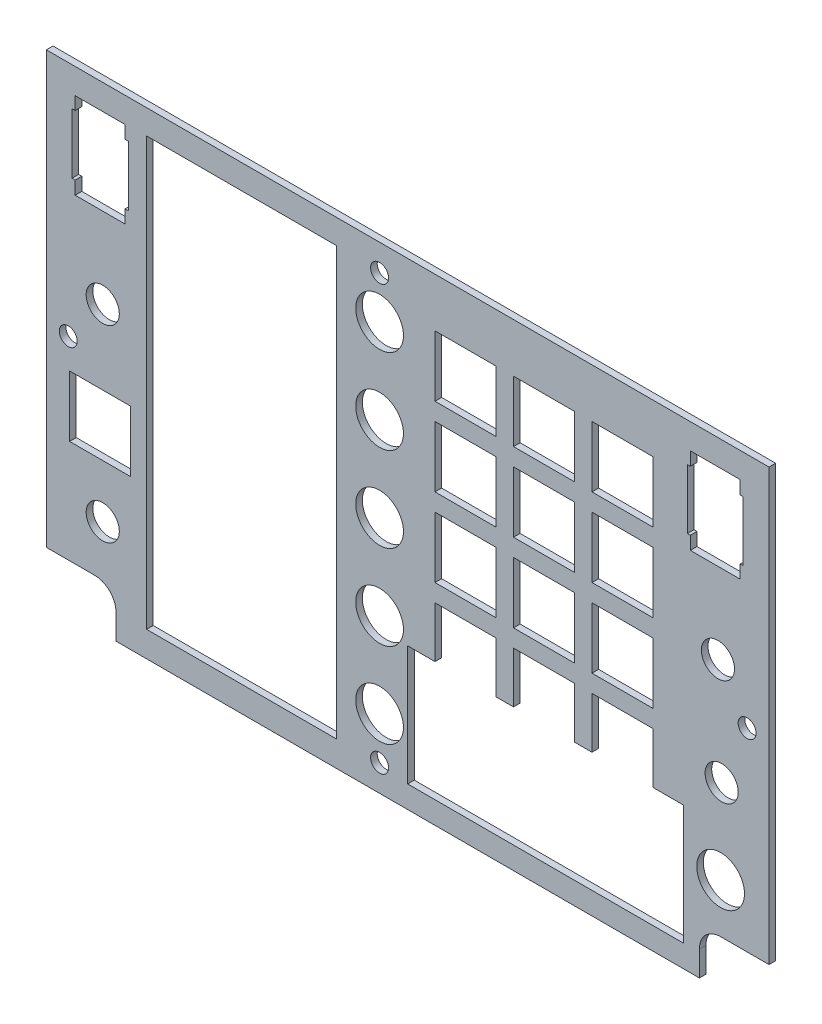
SolidWorks part; units mm, degrees
material "ABS PC"
ref_plane "Front Plane" through (0, 0, 0) normal (0, 0, 1) x (1, 0, 0)
ref_plane "Top Plane" through (0, 0, 0) normal (0, 1, 0) x (1, 0, 0)
ref_plane "Right Plane" through (0, 0, 0) normal (1, 0, 0) x (0, 0, -1)
sketch "Sketch1" plane through (0, 0, 0) normal (0, 0, 1) x (1, 0, 0)
  line L8 (74.93, -171.1167) -> (86.5187, -171.1167)
  line L9 (86.5187, -171.1167) -> (86.5187, -67.9292)
  line L10 (86.5187, -67.9292) -> (-86.5187, -67.9292)
  line L11 (-86.5187, -67.9292) -> (-86.5187, -171.1167)
  line L12 (-86.5187, -171.1167) -> (-74.93, -171.1167)
  line L13 (-69.85, -176.1967) -> (-69.85, -182.2292)
  line L14 (-69.85, -182.2292) -> (69.85, -182.2292)
  line L15 (69.85, -182.2292) -> (69.85, -176.1967)
  line L16 (74.93, -171.1167) -> (86.5187, -171.1167)
  line L17 (86.5187, -171.1167) -> (86.5187, -67.9292)
  line L18 (86.5187, -67.9292) -> (-86.5187, -67.9292)
  line L19 (-86.5187, -67.9292) -> (-86.5187, -171.1167)
  line L20 (-86.5187, -171.1167) -> (-74.93, -171.1167)
  line L21 (-69.85, -176.1967) -> (-69.85, -182.2292)
  line L22 (-69.85, -182.2292) -> (69.85, -182.2292)
  line L23 (69.85, -182.2292) -> (69.85, -176.1967)
  arc A2 (-69.85, -176.1967) -> (-74.93, -171.1167) centre (-74.93, -176.1967) ccw
  arc A3 (74.93, -171.1167) -> (69.85, -176.1967) centre (74.93, -176.1967) ccw
  arc A4 (-69.85, -176.1967) -> (-74.93, -171.1167) centre (-74.93, -176.1967) ccw
  arc A5 (74.93, -171.1167) -> (69.85, -176.1967) centre (74.93, -176.1967) ccw
  dimension "D1" = 0
extrude "Boss-Extrude1" add sketch "Sketch1" against normal blind 1.5875
sketch "Sketch3" plane through (0, 0, 0) normal (0, 0, 1) x (1, 0, 0)
  line L0 (-67.6275, -133.0167) -> (-79.6925, -133.0167) construction
  line L1 (-79.6925, -133.0167) -> (-79.6925, -145.0817) construction
  line L2 (-79.6925, -145.0817) -> (-67.6275, -145.0817) construction
  line L3 (-67.6275, -145.0817) -> (-67.6275, -133.0167) construction
  line L4 (19.8755, -149.3997) -> (19.8755, -137.3347) construction
  line L5 (19.8755, -137.3347) -> (7.8105, -137.3347) construction
  line L6 (7.8105, -137.3347) -> (7.8105, -149.3997) construction
  line L7 (7.8105, -149.3997) -> (19.8755, -149.3997) construction
  line L8 (38.6715, -149.3997) -> (38.6715, -137.3347) construction
  line L9 (38.6715, -137.3347) -> (26.6065, -137.3347) construction
  line L10 (26.6065, -137.3347) -> (26.6065, -149.3997) construction
  line L11 (26.6065, -149.3997) -> (38.6715, -149.3997) construction
  line L12 (45.4025, -149.3997) -> (57.4675, -149.3997) construction
  line L13 (57.4675, -149.3997) -> (57.4675, -137.3347) construction
  line L14 (57.4675, -137.3347) -> (45.4025, -137.3347) construction
  line L15 (45.4025, -137.3347) -> (45.4025, -149.3997) construction
  line L16 (57.4675, -130.6037) -> (57.4675, -118.5387) construction
  line L17 (57.4675, -118.5387) -> (45.4025, -118.5387) construction
  line L18 (45.4025, -118.5387) -> (45.4025, -130.6037) construction
  line L19 (45.4025, -130.6037) -> (57.4675, -130.6037) construction
  line L20 (38.6715, -130.6037) -> (38.6715, -118.5387) construction
  line L21 (38.6715, -118.5387) -> (26.6065, -118.5387) construction
  line L22 (26.6065, -118.5387) -> (26.6065, -130.6037) construction
  line L23 (26.6065, -130.6037) -> (38.6715, -130.6037) construction
  line L24 (19.8755, -130.6037) -> (19.8755, -118.5387) construction
  line L25 (19.8755, -118.5387) -> (7.8105, -118.5387) construction
  line L26 (7.8105, -118.5387) -> (7.8105, -130.6037) construction
  line L27 (7.8105, -130.6037) -> (19.8755, -130.6037) construction
  line L28 (19.8755, -111.8077) -> (19.8755, -99.7427) construction
  line L29 (19.8755, -99.7427) -> (7.8105, -99.7427) construction
  line L30 (7.8105, -99.7427) -> (7.8105, -111.8077) construction
  line L31 (7.8105, -111.8077) -> (19.8755, -111.8077) construction
  line L32 (19.8755, -93.0117) -> (19.8755, -80.9467) construction
  line L33 (19.8755, -80.9467) -> (7.8105, -80.9467) construction
  line L34 (7.8105, -80.9467) -> (7.8105, -93.0117) construction
  line L35 (7.8105, -93.0117) -> (19.8755, -93.0117) construction
  line L36 (38.6715, -93.0117) -> (38.6715, -80.9467) construction
  line L37 (38.6715, -80.9467) -> (26.6065, -80.9467) construction
  line L38 (26.6065, -80.9467) -> (26.6065, -93.0117) construction
  line L39 (26.6065, -93.0117) -> (38.6715, -93.0117) construction
  line L40 (38.6715, -111.8077) -> (38.6715, -99.7427) construction
  line L41 (38.6715, -99.7427) -> (26.6065, -99.7427) construction
  line L42 (26.6065, -99.7427) -> (26.6065, -111.8077) construction
  line L43 (26.6065, -111.8077) -> (38.6715, -111.8077) construction
  line L44 (57.4675, -111.8077) -> (57.4675, -99.7427) construction
  line L45 (57.4675, -99.7427) -> (45.4025, -99.7427) construction
  line L46 (45.4025, -99.7427) -> (45.4025, -111.8077) construction
  line L47 (45.4025, -111.8077) -> (57.4675, -111.8077) construction
  line L48 (57.4675, -93.0117) -> (57.4675, -80.9467) construction
  line L49 (57.4675, -80.9467) -> (45.4025, -80.9467) construction
  line L50 (45.4025, -80.9467) -> (45.4025, -93.0117) construction
  line L51 (45.4025, -93.0117) -> (57.4675, -93.0117) construction
  line L52 (-67.6275, -133.0167) -> (-79.6925, -133.0167)
  line L53 (-79.6925, -133.0167) -> (-79.6925, -145.0817)
  line L54 (-79.6925, -145.0817) -> (-67.6275, -145.0817)
  line L55 (-67.6275, -145.0817) -> (-67.6275, -133.0167)
  line L56 (19.8755, -149.3997) -> (19.8755, -137.3347)
  line L57 (19.8755, -137.3347) -> (7.8105, -137.3347)
  line L58 (7.8105, -137.3347) -> (7.8105, -149.3997)
  line L59 (7.8105, -149.3997) -> (19.8755, -149.3997)
  line L60 (38.6715, -149.3997) -> (38.6715, -137.3347)
  line L61 (38.6715, -137.3347) -> (26.6065, -137.3347)
  line L62 (26.6065, -137.3347) -> (26.6065, -149.3997)
  line L63 (26.6065, -149.3997) -> (38.6715, -149.3997)
  line L64 (45.4025, -149.3997) -> (57.4675, -149.3997)
  line L65 (57.4675, -149.3997) -> (57.4675, -137.3347)
  line L66 (57.4675, -137.3347) -> (45.4025, -137.3347)
  line L67 (45.4025, -137.3347) -> (45.4025, -149.3997)
  line L68 (57.4675, -130.6037) -> (57.4675, -118.5387)
  line L69 (57.4675, -118.5387) -> (45.4025, -118.5387)
  line L70 (45.4025, -118.5387) -> (45.4025, -130.6037)
  line L71 (45.4025, -130.6037) -> (57.4675, -130.6037)
  line L72 (38.6715, -130.6037) -> (38.6715, -118.5387)
  line L73 (38.6715, -118.5387) -> (26.6065, -118.5387)
  line L74 (26.6065, -118.5387) -> (26.6065, -130.6037)
  line L75 (26.6065, -130.6037) -> (38.6715, -130.6037)
  line L76 (19.8755, -130.6037) -> (19.8755, -118.5387)
  line L77 (19.8755, -118.5387) -> (7.8105, -118.5387)
  line L78 (7.8105, -118.5387) -> (7.8105, -130.6037)
  line L79 (7.8105, -130.6037) -> (19.8755, -130.6037)
  line L80 (19.8755, -111.8077) -> (19.8755, -99.7427)
  line L81 (19.8755, -99.7427) -> (7.8105, -99.7427)
  line L82 (7.8105, -99.7427) -> (7.8105, -111.8077)
  line L83 (7.8105, -111.8077) -> (19.8755, -111.8077)
  line L84 (19.8755, -93.0117) -> (19.8755, -80.9467)
  line L85 (19.8755, -80.9467) -> (7.8105, -80.9467)
  line L86 (7.8105, -80.9467) -> (7.8105, -93.0117)
  line L87 (7.8105, -93.0117) -> (19.8755, -93.0117)
  line L88 (38.6715, -93.0117) -> (38.6715, -80.9467)
  line L89 (38.6715, -80.9467) -> (26.6065, -80.9467)
  line L90 (26.6065, -80.9467) -> (26.6065, -93.0117)
  line L91 (26.6065, -93.0117) -> (38.6715, -93.0117)
  line L92 (38.6715, -111.8077) -> (38.6715, -99.7427)
  line L93 (38.6715, -99.7427) -> (26.6065, -99.7427)
  line L94 (26.6065, -99.7427) -> (26.6065, -111.8077)
  line L95 (26.6065, -111.8077) -> (38.6715, -111.8077)
  line L96 (57.4675, -111.8077) -> (57.4675, -99.7427)
  line L97 (57.4675, -99.7427) -> (45.4025, -99.7427)
  line L98 (45.4025, -99.7427) -> (45.4025, -111.8077)
  line L99 (45.4025, -111.8077) -> (57.4675, -111.8077)
  line L100 (57.4675, -93.0117) -> (57.4675, -80.9467)
  line L101 (57.4675, -80.9467) -> (45.4025, -80.9467)
  line L102 (45.4025, -80.9467) -> (45.4025, -93.0117)
  line L103 (45.4025, -93.0117) -> (57.4675, -93.0117)
  circle A0 centre (74.93, -159.3692) radius 4.445 construction
  circle A1 centre (-6.731, -165.7192) radius 4.445 construction
  circle A2 centre (-6.731, -145.3992) radius 4.445 construction
  circle A3 centre (-6.731, -125.0792) radius 4.445 construction
  circle A4 centre (-6.731, -104.7592) radius 4.445 construction
  circle A5 centre (-6.731, -84.4392) radius 4.445 construction
  circle A6 centre (74.93, -159.3692) radius 4.445
  circle A7 centre (-6.731, -165.7192) radius 4.445
  circle A8 centre (-6.731, -145.3992) radius 4.445
  circle A9 centre (-6.731, -125.0792) radius 4.445
  circle A10 centre (-6.731, -104.7592) radius 4.445
  circle A11 centre (-6.731, -84.4392) radius 4.445
extrude "Cut-Extrude1" cut sketch "Sketch3" against normal through all
sketch "Sketch4" plane through (0, 0, 0) normal (0, 0, 1) x (1, 0, 0)
  circle A0 centre (-73.025, -113.9667) radius 3.9688
  circle A1 centre (-73.025, -159.0517) radius 3.9688
  circle A2 centre (74.295, -113.9667) radius 3.9688
  circle A3 centre (75.184, -139.0492) radius 3.9687
  dimension "D1" = 7.9375
extrude "Cut-Extrude2" cut sketch "Sketch4" against normal through all
sketch "Sketch5" plane through (0, 0, 0) normal (0, 0, 1) x (1, 0, 0)
  line L0 (-79.63, -73.9922) -> (-79.63, -94.6322)
  line L1 (-79.63, -94.6322) -> (-67.69, -94.6322)
  line L2 (-67.69, -94.6322) -> (-67.69, -73.9922)
  line L3 (-67.69, -73.9922) -> (-79.63, -73.9922)
  line L4 (-78.36, -75.2622) -> (-78.36, -93.3622)
  line L5 (-78.36, -93.3622) -> (-68.96, -93.3622)
  line L6 (-68.96, -93.3622) -> (-68.96, -75.2622)
  line L7 (-68.96, -75.2622) -> (-78.36, -75.2622)
  line L8 (-78.36, -75.2622) -> (-78.36, -93.3622) construction
  line L9 (-78.36, -93.3622) -> (-68.96, -93.3622) construction
  line L10 (-68.96, -93.3622) -> (-68.96, -75.2622) construction
  line L11 (-68.96, -75.2622) -> (-78.36, -75.2622) construction
  line L12 (68.96, -75.2622) -> (68.96, -93.3622)
  line L13 (68.96, -93.3622) -> (78.36, -93.3622)
  line L14 (78.36, -93.3622) -> (78.36, -75.2622)
  line L15 (78.36, -75.2622) -> (68.96, -75.2622)
  line L16 (68.96, -75.2622) -> (68.96, -93.3622) construction
  line L17 (68.96, -93.3622) -> (78.36, -93.3622) construction
  line L18 (78.36, -93.3622) -> (78.36, -75.2622) construction
  line L19 (78.36, -75.2622) -> (68.96, -75.2622) construction
  line L20 (67.69, -73.9922) -> (67.69, -94.6322)
  line L21 (67.69, -94.6322) -> (79.63, -94.6322)
  line L22 (79.63, -94.6322) -> (79.63, -73.9922)
  line L23 (79.63, -73.9922) -> (67.69, -73.9922)
  line L24 (-61.06, -75.0622) -> (-51.66, -75.0622) construction
  line L25 (-62.53, -73.7922) -> (-17.068, -73.7922)
  line L26 (-62.53, -73.7922) -> (-62.53, -176.1122)
  line L27 (-62.53, -176.1122) -> (-17.068, -176.1122)
  line L28 (-17.068, -73.7922) -> (-17.068, -176.1122)
  line L29 (-62.53, -73.7922) -> (-17.068, -176.1122) construction
  line L30 (-62.53, -176.1122) -> (-17.068, -73.7922) construction
  line L31 (-61.26, -93.3622) -> (-61.26, -75.2622) construction
  line L32 (-51.66, -174.8422) -> (-61.06, -174.8422) construction
  line L33 (-18.338, -167.7344) -> (-18.338, -169.4031) construction
  line L34 (61.52, -158.4422) -> (61.52, -172.5422) construction
  line L35 (5.02, -157.9422) -> (61.02, -157.9422) construction
  line L36 (61.02, -173.0422) -> (5.02, -173.0422) construction
  line L37 (4.52, -172.5422) -> (4.52, -158.4422) construction
  line L38 (61.52, -157.9422) -> (61.52, -173.0422)
  line L39 (4.52, -157.9422) -> (61.52, -157.9422)
  line L40 (61.52, -173.0422) -> (4.52, -173.0422)
  line L41 (4.52, -173.0422) -> (4.52, -157.9422)
  point P20 (-39.799, -124.9522)
  dimension "D4" = 1.27
  dimension "D5" = 1.27
  dimension "D6" = 1.27
  dimension "D7" = 1.27
  dimension "D1" = 0
  dimension "D2" = 0
  dimension "D3" = 1.27
extrude "Cut-Extrude3" cut sketch "Sketch5" against normal through all
sketch "Sketch6" plane through (0, 0, 0) normal (0, 0, 1) x (1, 0, 0)
  line L4 (-67.6275, -133.0167) -> (-79.6925, -133.0167) construction
  line L5 (57.4675, -137.3347) -> (45.4025, -137.3347) construction
  line L6 (45.4025, -137.3347) -> (45.4025, -149.3997) construction
  line L7 (45.4025, -149.3997) -> (57.4675, -149.3997) construction
  line L8 (57.4675, -149.3997) -> (57.4675, -137.3347) construction
  line L9 (45.4025, -130.6037) -> (57.4675, -130.6037) construction
  line L10 (57.4675, -130.6037) -> (57.4675, -118.5387) construction
  line L11 (57.4675, -118.5387) -> (45.4025, -118.5387) construction
  line L12 (45.4025, -118.5387) -> (45.4025, -130.6037) construction
  line L13 (45.4025, -111.8077) -> (57.4675, -111.8077) construction
  line L14 (57.4675, -111.8077) -> (57.4675, -99.7427) construction
  line L15 (57.4675, -99.7427) -> (45.4025, -99.7427) construction
  line L16 (45.4025, -99.7427) -> (45.4025, -111.8077) construction
  line L17 (45.4025, -93.0117) -> (57.4675, -93.0117) construction
  line L18 (57.4675, -93.0117) -> (57.4675, -80.9467) construction
  line L19 (57.4675, -80.9467) -> (45.4025, -80.9467) construction
  line L20 (45.4025, -80.9467) -> (45.4025, -93.0117) construction
  line L21 (26.6065, -149.3997) -> (38.6715, -149.3997) construction
  line L22 (38.6715, -149.3997) -> (38.6715, -137.3347) construction
  line L23 (38.6715, -137.3347) -> (26.6065, -137.3347) construction
  line L24 (26.6065, -137.3347) -> (26.6065, -149.3997) construction
  line L25 (26.6065, -130.6037) -> (38.6715, -130.6037) construction
  line L26 (38.6715, -130.6037) -> (38.6715, -118.5387) construction
  line L27 (38.6715, -118.5387) -> (26.6065, -118.5387) construction
  line L28 (26.6065, -118.5387) -> (26.6065, -130.6037) construction
  line L29 (26.6065, -111.8077) -> (38.6715, -111.8077) construction
  line L30 (38.6715, -111.8077) -> (38.6715, -99.7427) construction
  line L31 (38.6715, -99.7427) -> (26.6065, -99.7427) construction
  line L32 (26.6065, -99.7427) -> (26.6065, -111.8077) construction
  line L33 (26.6065, -93.0117) -> (38.6715, -93.0117) construction
  line L34 (38.6715, -93.0117) -> (38.6715, -80.9467) construction
  line L35 (38.6715, -80.9467) -> (26.6065, -80.9467) construction
  line L36 (26.6065, -80.9467) -> (26.6065, -93.0117) construction
  line L37 (7.8105, -93.0117) -> (19.8755, -93.0117) construction
  line L38 (19.8755, -93.0117) -> (19.8755, -80.9467) construction
  line L39 (19.8755, -80.9467) -> (7.8105, -80.9467) construction
  line L40 (7.8105, -80.9467) -> (7.8105, -93.0117) construction
  line L41 (7.8105, -111.8077) -> (19.8755, -111.8077) construction
  line L42 (19.8755, -111.8077) -> (19.8755, -99.7427) construction
  line L43 (19.8755, -99.7427) -> (7.8105, -99.7427) construction
  line L44 (7.8105, -99.7427) -> (7.8105, -111.8077) construction
  line L45 (19.8755, -118.5387) -> (7.8105, -118.5387) construction
  line L46 (7.8105, -118.5387) -> (7.8105, -130.6037) construction
  line L47 (7.8105, -130.6037) -> (19.8755, -130.6037) construction
  line L48 (19.8755, -130.6037) -> (19.8755, -118.5387) construction
  line L49 (19.8755, -137.3347) -> (7.8105, -137.3347) construction
  line L50 (7.8105, -137.3347) -> (7.8105, -149.3997) construction
  line L51 (7.8105, -149.3997) -> (19.8755, -149.3997) construction
  line L52 (19.8755, -149.3997) -> (19.8755, -137.3347) construction
  line L53 (-79.6925, -133.0167) -> (-79.6925, -145.0817) construction
  line L54 (-79.6925, -145.0817) -> (-67.6275, -145.0817) construction
  line L55 (-67.6275, -145.0817) -> (-67.6275, -133.0167) construction
  line L56 (57.4675, -137.3347) -> (45.4025, -137.3347) construction
  line L57 (45.4025, -137.3347) -> (45.4025, -149.3997) construction
  line L58 (45.4025, -149.3997) -> (57.4675, -149.3997) construction
  line L59 (57.4675, -149.3997) -> (57.4675, -137.3347) construction
  line L60 (45.4025, -130.6037) -> (57.4675, -130.6037) construction
  line L61 (57.4675, -130.6037) -> (57.4675, -118.5387) construction
  line L62 (57.4675, -118.5387) -> (45.4025, -118.5387) construction
  line L63 (45.4025, -118.5387) -> (45.4025, -130.6037) construction
  line L64 (45.4025, -111.8077) -> (57.4675, -111.8077) construction
  line L65 (57.4675, -111.8077) -> (57.4675, -99.7427) construction
  line L66 (57.4675, -99.7427) -> (45.4025, -99.7427) construction
  line L67 (45.4025, -99.7427) -> (45.4025, -111.8077) construction
  line L68 (45.4025, -93.0117) -> (57.4675, -93.0117) construction
  line L69 (57.4675, -93.0117) -> (57.4675, -80.9467) construction
  line L70 (57.4675, -80.9467) -> (45.4025, -80.9467) construction
  line L71 (45.4025, -80.9467) -> (45.4025, -93.0117) construction
  line L72 (26.6065, -149.3997) -> (38.6715, -149.3997) construction
  line L73 (38.6715, -149.3997) -> (38.6715, -137.3347) construction
  line L74 (38.6715, -137.3347) -> (26.6065, -137.3347) construction
  line L75 (26.6065, -137.3347) -> (26.6065, -149.3997) construction
  line L76 (26.6065, -130.6037) -> (38.6715, -130.6037) construction
  line L77 (38.6715, -130.6037) -> (38.6715, -118.5387) construction
  line L78 (38.6715, -118.5387) -> (26.6065, -118.5387) construction
  line L79 (26.6065, -118.5387) -> (26.6065, -130.6037) construction
  line L80 (26.6065, -111.8077) -> (38.6715, -111.8077) construction
  line L81 (38.6715, -111.8077) -> (38.6715, -99.7427) construction
  line L82 (38.6715, -99.7427) -> (26.6065, -99.7427) construction
  line L83 (26.6065, -99.7427) -> (26.6065, -111.8077) construction
  line L84 (26.6065, -93.0117) -> (38.6715, -93.0117) construction
  line L85 (38.6715, -93.0117) -> (38.6715, -80.9467) construction
  line L86 (38.6715, -80.9467) -> (26.6065, -80.9467) construction
  line L87 (26.6065, -80.9467) -> (26.6065, -93.0117) construction
  line L88 (7.8105, -93.0117) -> (19.8755, -93.0117) construction
  line L89 (19.8755, -93.0117) -> (19.8755, -80.9467) construction
  line L90 (19.8755, -80.9467) -> (7.8105, -80.9467) construction
  line L91 (7.8105, -80.9467) -> (7.8105, -93.0117) construction
  line L92 (7.8105, -111.8077) -> (19.8755, -111.8077) construction
  line L93 (19.8755, -111.8077) -> (19.8755, -99.7427) construction
  line L94 (19.8755, -99.7427) -> (7.8105, -99.7427) construction
  line L95 (7.8105, -99.7427) -> (7.8105, -111.8077) construction
  line L96 (19.8755, -118.5387) -> (7.8105, -118.5387) construction
  line L97 (7.8105, -118.5387) -> (7.8105, -130.6037) construction
  line L98 (7.8105, -130.6037) -> (19.8755, -130.6037) construction
  line L99 (19.8755, -130.6037) -> (19.8755, -118.5387) construction
  line L100 (19.8755, -137.3347) -> (7.8105, -137.3347) construction
  line L101 (7.8105, -137.3347) -> (7.8105, -149.3997) construction
  line L102 (7.8105, -149.3997) -> (19.8755, -149.3997) construction
  line L103 (19.8755, -149.3997) -> (19.8755, -137.3347) construction
  line L104 (-67.6275, -133.0167) -> (-79.6925, -133.0167) construction
  line L105 (-79.6925, -133.0167) -> (-79.6925, -145.0817) construction
  line L106 (-79.6925, -145.0817) -> (-67.6275, -145.0817) construction
  line L107 (-67.6275, -145.0817) -> (-67.6275, -133.0167) construction
  line L108 (58.7375, -136.0647) -> (44.1325, -136.0647)
  line L109 (44.1325, -136.0647) -> (44.1325, -150.6697)
  line L110 (44.1325, -150.6697) -> (58.7375, -150.6697)
  line L111 (58.7375, -150.6697) -> (58.7375, -136.0647)
  line L112 (44.1325, -131.8737) -> (58.7375, -131.8737)
  line L113 (58.7375, -131.8737) -> (58.7375, -117.2687)
  line L114 (58.7375, -117.2687) -> (44.1325, -117.2687)
  line L115 (44.1325, -117.2687) -> (44.1325, -131.8737)
  line L116 (44.1325, -113.0777) -> (58.7375, -113.0777)
  line L117 (58.7375, -113.0777) -> (58.7375, -98.4727)
  line L118 (58.7375, -98.4727) -> (44.1325, -98.4727)
  line L119 (44.1325, -98.4727) -> (44.1325, -113.0777)
  line L120 (44.1325, -94.2817) -> (58.7375, -94.2817)
  line L121 (58.7375, -94.2817) -> (58.7375, -79.6767)
  line L122 (58.7375, -79.6767) -> (44.1325, -79.6767)
  line L123 (44.1325, -79.6767) -> (44.1325, -94.2817)
  line L124 (25.3365, -150.6697) -> (39.9415, -150.6697)
  line L125 (39.9415, -150.6697) -> (39.9415, -136.0647)
  line L126 (39.9415, -136.0647) -> (25.3365, -136.0647)
  line L127 (25.3365, -136.0647) -> (25.3365, -150.6697)
  line L128 (25.3365, -131.8737) -> (39.9415, -131.8737)
  line L129 (39.9415, -131.8737) -> (39.9415, -117.2687)
  line L130 (39.9415, -117.2687) -> (25.3365, -117.2687)
  line L131 (25.3365, -117.2687) -> (25.3365, -131.8737)
  line L132 (25.3365, -113.0777) -> (39.9415, -113.0777)
  line L133 (39.9415, -113.0777) -> (39.9415, -98.4727)
  line L134 (39.9415, -98.4727) -> (25.3365, -98.4727)
  line L135 (25.3365, -98.4727) -> (25.3365, -113.0777)
  line L136 (25.3365, -94.2817) -> (39.9415, -94.2817)
  line L137 (39.9415, -94.2817) -> (39.9415, -79.6767)
  line L138 (39.9415, -79.6767) -> (25.3365, -79.6767)
  line L139 (25.3365, -79.6767) -> (25.3365, -94.2817)
  line L140 (6.5405, -94.2817) -> (21.1455, -94.2817)
  line L141 (21.1455, -94.2817) -> (21.1455, -79.6767)
  line L142 (21.1455, -79.6767) -> (6.5405, -79.6767)
  line L143 (6.5405, -79.6767) -> (6.5405, -94.2817)
  line L144 (6.5405, -113.0777) -> (21.1455, -113.0777)
  line L145 (21.1455, -113.0777) -> (21.1455, -98.4727)
  line L146 (21.1455, -98.4727) -> (6.5405, -98.4727)
  line L147 (6.5405, -98.4727) -> (6.5405, -113.0777)
  line L148 (21.1455, -117.2687) -> (6.5405, -117.2687)
  line L149 (6.5405, -117.2687) -> (6.5405, -131.8737)
  line L150 (6.5405, -131.8737) -> (21.1455, -131.8737)
  line L151 (21.1455, -131.8737) -> (21.1455, -117.2687)
  line L152 (21.1455, -136.0647) -> (6.5405, -136.0647)
  line L153 (6.5405, -136.0647) -> (6.5405, -150.6697)
  line L154 (6.5405, -150.6697) -> (21.1455, -150.6697)
  line L155 (21.1455, -150.6697) -> (21.1455, -136.0647)
  line L156 (-66.3575, -131.7467) -> (-80.9625, -131.7467)
  line L157 (-80.9625, -131.7467) -> (-80.9625, -146.3517)
  line L158 (-80.9625, -146.3517) -> (-66.3575, -146.3517)
  line L159 (-66.3575, -146.3517) -> (-66.3575, -131.7467)
  circle A6 centre (74.93, -159.3692) radius 4.445 construction
  circle A7 centre (-6.731, -165.7192) radius 4.445 construction
  circle A9 centre (-6.731, -145.3992) radius 4.445 construction
  circle A12 centre (-6.731, -125.0792) radius 4.445 construction
  circle A16 centre (-6.731, -104.7592) radius 4.445 construction
  circle A21 centre (-6.731, -84.4392) radius 4.445 construction
  circle A33 centre (74.93, -159.3692) radius 4.445 construction
  circle A34 centre (-6.731, -165.7192) radius 4.445 construction
  circle A35 centre (-6.731, -145.3992) radius 4.445 construction
  circle A36 centre (-6.731, -125.0792) radius 4.445 construction
  circle A37 centre (-6.731, -104.7592) radius 4.445 construction
  circle A38 centre (-6.731, -84.4392) radius 4.445 construction
  circle A39 centre (74.93, -159.3692) radius 5.715
  circle A40 centre (-6.731, -165.7192) radius 5.715
  circle A41 centre (-6.731, -145.3992) radius 5.715
  circle A42 centre (-6.731, -125.0792) radius 5.715
  circle A43 centre (-6.731, -104.7592) radius 5.715
  circle A44 centre (-6.731, -84.4392) radius 5.715
  dimension "D1" = 1.27
extrude "Cut-Extrude4" cut sketch "Sketch6" against normal through all
sketch "Sketch7" plane through (0, 0, 0) normal (0, 0, 1) x (1, 0, 0)
  line L0 (66.04, -176.9122) -> (66.04, -148.2722)
  line L1 (66.04, -148.2722) -> (0, -148.2722)
  line L2 (0, -148.2722) -> (0, -176.9122)
  line L3 (0, -176.9122) -> (66.04, -176.9122)
  line L4 (64.77, -175.6422) -> (64.77, -149.5422)
  line L5 (64.77, -149.5422) -> (1.27, -149.5422)
  line L6 (1.27, -149.5422) -> (1.27, -175.6422)
  line L7 (1.27, -175.6422) -> (64.77, -175.6422)
  line L8 (64.77, -175.6422) -> (64.77, -149.5422) construction
  line L9 (64.77, -149.5422) -> (1.27, -149.5422) construction
  line L10 (1.27, -149.5422) -> (1.27, -175.6422) construction
  line L11 (1.27, -175.6422) -> (64.77, -175.6422) construction
  dimension "D1" = 0
  dimension "D2" = 1.27
extrude "Cut-Extrude5" cut sketch "Sketch7" against normal through all
hole_wizard "#6 Clearance Hole2" positions "Sketch10" profile "Sketch11" hole size "#6" standard "ANSI Inch" end condition through all
sketch "Sketch10" plane through (0, 0, 1.5875) normal (0, 0, 1) x (-1, 0, 0)
  point P0 (-81.28, 124.6982)
  point P3 (6.731, 175.8792)
  point P6 (81.28, 124.6982)
  point P9 (6.731, 74.2792)
sketch "Sketch11" plane through (81.28, -124.6982, 1.5875) normal (1, 0, 0) x (0, -1, 0)
  line L0 (0, 0) -> (0, 3.175)
  line L1 (0, 3.175) -> (2.1526, 3.175)
  line L2 (2.1526, 3.175) -> (2.1526, 0)
  line L3 (2.1526, 0) -> (0, 0)
  line L4 (0, -6.35) -> (0, 107.95) construction
  dimension "Thru Hole Dia." = 4.3053
  dimension "Thru Hole Depth" = 3.175
sketch "Sketch12" plane through (0, 0, -1.5875) normal (0, 0, -1) x (-1, 0, 0)
  line L4 (66.848, -77.0669) -> (66.848, -91.4915)
  line L5 (80.377, -77.0669) -> (66.848, -77.0669)
  line L6 (66.848, -91.4915) -> (80.377, -91.4915)
  line L7 (80.377, -91.4915) -> (80.377, -77.0669)
  line L10 (-80.3146, -77.1801) -> (-80.3146, -91.4929)
  line L11 (-66.9818, -91.4929) -> (-66.9818, -77.1801)
  line L12 (-66.9818, -91.4929) -> (-80.3146, -91.4929)
  line L13 (-80.3146, -77.1801) -> (-66.9818, -77.1801)
extrude "Cut-Extrude6" cut sketch "Sketch12" against normal up to next
